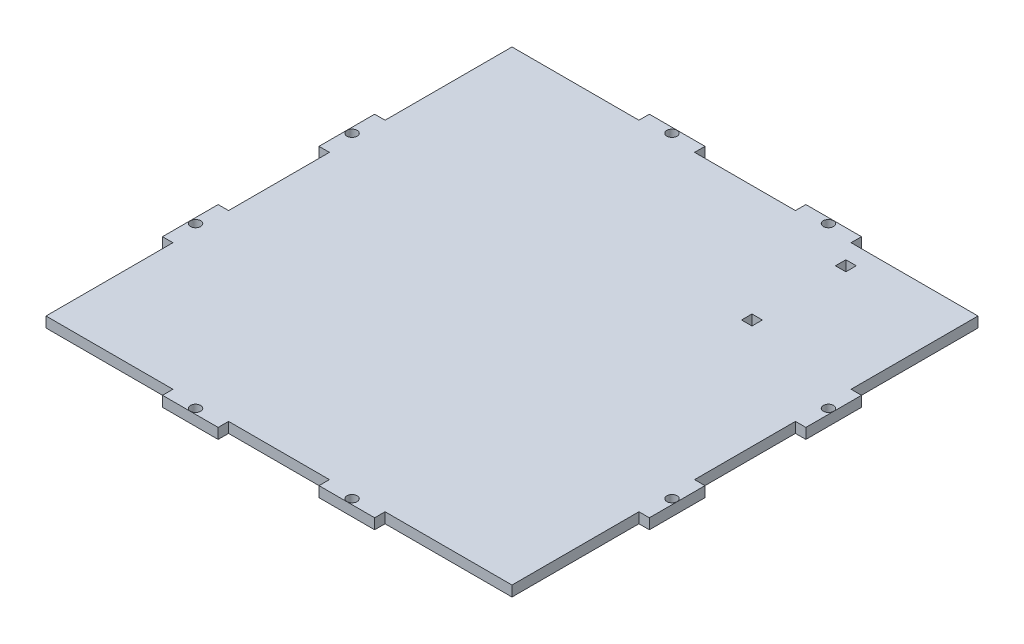
SolidWorks part; units mm, degrees
ref_plane "Front Plane" through (0, 0, 0) normal (0, 0, 1) x (1, 0, 0)
ref_plane "Top Plane" through (0, 0, 0) normal (0, 1, 0) x (1, 0, 0)
ref_plane "Right Plane" through (0, 0, 0) normal (1, 0, 0) x (0, 0, -1)
sketch "Sketch1" plane through (0, 0, 0) normal (0, 1, 0) x (1, 0, 0)
  line L0 (-70, 70) -> (70, -70)
  line L1 (-70, 70) -> (70, 70)
  line L2 (-70, 70) -> (-70, -70)
  line L3 (-70, -70) -> (70, -70)
  line L4 (70, 70) -> (70, -70)
  line L5 (-70, -70) -> (70, 70)
  point P4 (0, 0)
  dimension "D1" = 140
  dimension "D2" = 140
extrude "Boss-Extrude1" add sketch "Sketch1" along normal blind 3 contours L0 L5 L1 | L2 L5 L0 | L5 L3 L0 | L5 L0 L4
sketch "Sketch2" plane through (0, 3, 0) normal (0, 1, 0) x (1, 0, 0)
  line L0 (-70, 70) -> (-70, 67)
  line L1 (-70, 70) -> (-70, -70) construction
  line L2 (-70, 67) -> (-30.5, 67)
  line L3 (-30.5, 67) -> (-30.5, 70)
  line L4 (-70, 70) -> (70, 70) construction
  line L5 (-30.5, 70) -> (-70, 70)
  line L6 (0, -1.65) -> (0, 1.65) construction
  line L7 (30.5, 67) -> (30.5, 70)
  line L8 (70, 67) -> (30.5, 67)
  line L9 (70, 70) -> (70, 67)
  line L10 (30.5, 70) -> (70, 70)
  line L11 (-1.65, 0) -> (1.65, 0) construction
  line L12 (70, -67) -> (30.5, -67)
  line L13 (70, -70) -> (70, -67)
  line L14 (30.5, -70) -> (70, -70)
  line L15 (30.5, -67) -> (30.5, -70)
  line L16 (-30.5, -67) -> (-30.5, -70)
  line L17 (-70, -67) -> (-30.5, -67)
  line L18 (-70, -70) -> (-70, -67)
  line L19 (-30.5, -70) -> (-70, -70)
  line L20 (-67, 30.5) -> (-67, 70)
  line L21 (-67, 70) -> (-70, 70)
  line L22 (-70, 70) -> (-70, 30.5)
  line L23 (-70, 30.5) -> (-67, 30.5)
  line L24 (67, 70) -> (70, 70)
  line L25 (67, 30.5) -> (67, 70)
  line L26 (70, 30.5) -> (67, 30.5)
  line L27 (70, 70) -> (70, 30.5)
  line L28 (67, -70) -> (70, -70)
  line L29 (67, -30.5) -> (67, -70)
  line L30 (70, -30.5) -> (67, -30.5)
  line L31 (70, -70) -> (70, -30.5)
  line L32 (-67, -70) -> (-70, -70)
  line L33 (-67, -30.5) -> (-67, -70)
  line L34 (-70, -30.5) -> (-67, -30.5)
  line L35 (-70, -70) -> (-70, -30.5)
  line L36 (-14.5, 70) -> (-14.5, 67)
  line L37 (-14.5, 67) -> (14.5, 67)
  line L38 (14.5, 67) -> (14.5, 70)
  line L39 (14.5, 70) -> (-14.5, 70)
  line L40 (14.5, -67) -> (14.5, -70)
  line L41 (-14.5, -67) -> (14.5, -67)
  line L42 (-14.5, -70) -> (-14.5, -67)
  line L43 (14.5, -70) -> (-14.5, -70)
  line L44 (70, -14.5) -> (70, 14.5)
  line L45 (-70, 14.5) -> (-67, 14.5)
  line L46 (-67, 14.5) -> (-67, -14.5)
  line L47 (-67, -14.5) -> (-70, -14.5)
  line L48 (-70, -14.5) -> (-70, 14.5)
  line L49 (67, -14.5) -> (70, -14.5)
  line L50 (67, 14.5) -> (67, -14.5)
  line L51 (70, 14.5) -> (67, 14.5)
  dimension "D1" = 39.5
  dimension "D2" = 3
  dimension "D3" = 3
  dimension "D4" = 39.5
  dimension "D5" = 29
  dimension "D6" = 55.5
  dimension "D7" = 29
  dimension "D8" = 55.5
  dimension "D9" = 3
extrude "Cut-Extrude2" cut sketch "Sketch2" against normal blind 3 contours L0 L2 L3 L5 | L22 L23 L20 L21 | L48 L45 L46 L47 | L35 L34 L33 L32 | L18 L17 L16 L19 | L41 L40 L43 L42 | L13 L12 L15 L14 | L31 L30 L29 L28 | L50 L49 L44 L51 | L27 L26 L25 L24 | L9 L8 L7 L10 | L39 L36 L37 L38
sketch "Sketch3" plane through (0, 3, 0) normal (0, 1, 0) x (1, 0, 0)
  line L0 (-30.5, 68.5) -> (-14.5, 68.5) construction
  line L1 (-30.5, 67) -> (-30.5, 70) construction
  line L2 (-14.5, 70) -> (-14.5, 67) construction
  line L3 (0, -1.65) -> (0, 1.65) construction
  line L4 (-1.65, 0) -> (1.65, 0) construction
  line L5 (-68.5, 30.5) -> (-68.5, 14.5) construction
  line L6 (-70, 30.5) -> (-67, 30.5) construction
  line L7 (-70, 14.5) -> (-67, 14.5) construction
  circle A0 centre (-22.5, 68.5) radius 1.47
  circle A1 centre (22.5, 68.5) radius 1.47
  circle A2 centre (22.5, -68.5) radius 1.47
  circle A3 centre (-22.5, -68.5) radius 1.47
  circle A4 centre (-68.5, 22.5) radius 1.47
  circle A5 centre (-68.5, -22.5) radius 1.47
  circle A6 centre (68.5, -22.5) radius 1.47
  circle A7 centre (68.5, 22.5) radius 1.47
  dimension "D1" = 2.94
  dimension "D2" = 2.94
extrude "Cut-Extrude3" cut sketch "Sketch3" against normal blind 3
sketch "Sketch4" plane through (0, 3, 0) normal (0, 1, 0) x (1, 0, 0)
  line L0 (67, 30.5) -> (67, 67) construction
  line L1 (34, 62) -> (37, 62)
  line L2 (34, 62) -> (34, 59)
  line L3 (34, 59) -> (37, 59)
  line L4 (37, 62) -> (37, 59)
  line L5 (34, 35) -> (37, 35)
  line L6 (34, 35) -> (34, 32)
  line L7 (34, 32) -> (37, 32)
  line L8 (37, 35) -> (37, 32)
  line L9 (67, 67) -> (30.5, 67) construction
  dimension "D1" = 3
  dimension "D2" = 30
  dimension "D3" = 5
  dimension "D4" = 30
extrude "Cut-Extrude4" cut sketch "Sketch4" against normal blind 3
